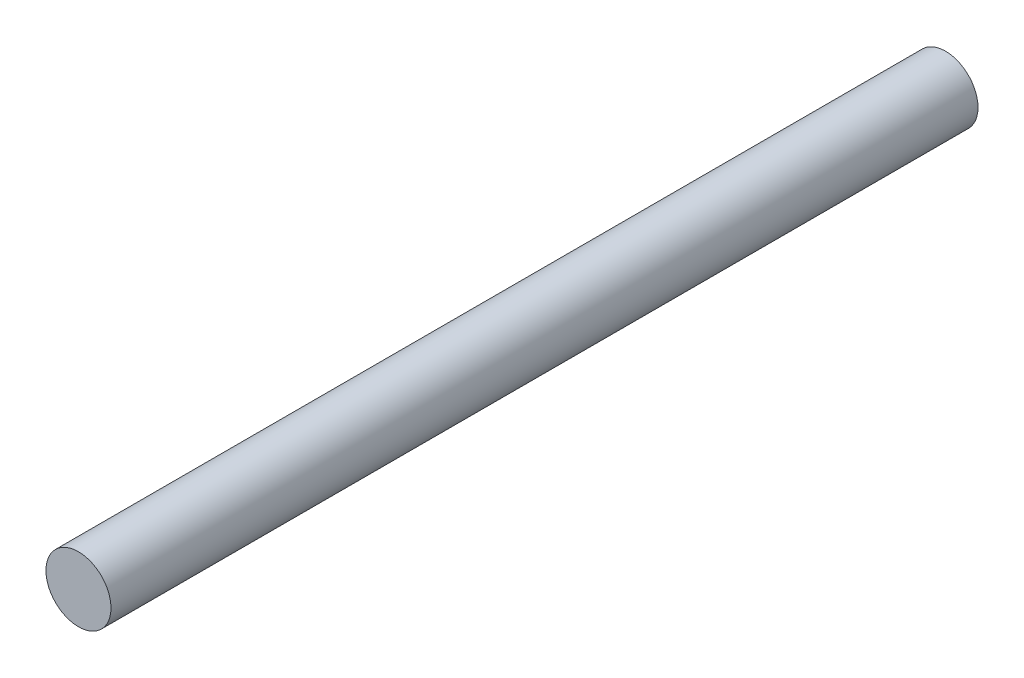
SolidWorks part; units mm, degrees
ref_plane "Front Plane" through (0, 0, 0) normal (0, 0, 1) x (1, 0, 0)
ref_plane "Top Plane" through (0, 0, 0) normal (0, 1, 0) x (1, 0, 0)
ref_plane "Right Plane" through (0, 0, 0) normal (1, 0, 0) x (0, 0, -1)
sketch "Sketch1" plane through (0, 0, 0) normal (0, 0, 1) x (1, 0, 0)
  circle A0 centre (0, 0) radius 3
  dimension "D1" = 6
extrude "Boss-Extrude1" add sketch "Sketch1" along normal blind 80
